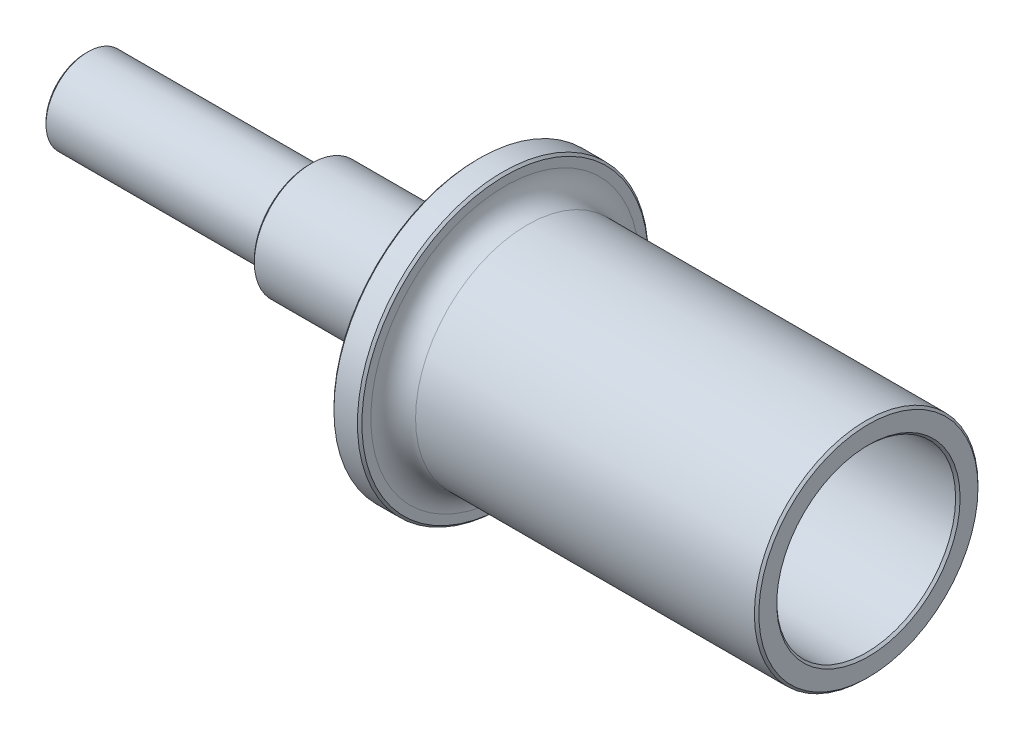
SolidWorks part; units mm, degrees
material "Plain Carbon Steel"
ref_plane "Front Plane" through (0, 0, 0) normal (0, 0, 1) x (1, 0, 0)
ref_plane "Top Plane" through (0, 0, 0) normal (0, 1, 0) x (1, 0, 0)
ref_plane "Right Plane" through (0, 0, 0) normal (1, 0, 0) x (0, 0, -1)
sketch "Sketch1" plane through (0, 0, 0) normal (0, 1, 0) x (1, 0, 0)
  line L0 (6.35, 10.16) -> (-31.6365, 10.16)
  line L1 (6.35, 10.16) -> (6.35, 12.7)
  line L2 (-38.1, 16.51) -> (-34.925, 16.51)
  line L3 (-38.1, 16.51) -> (-38.1, 6.5)
  line L4 (-38.1, 6.5) -> (-57.15, 6.5)
  line L5 (-57.15, 6.5) -> (-57.15, 4.7625)
  line L6 (-57.15, 4.7625) -> (-82.55, 4.7625)
  line L7 (-82.55, 0) -> (-82.55, 4.7625)
  line L8 (-34.1765, 7.62) -> (-34.1765, 0)
  line L9 (-34.925, 16.51) -> (-34.925, 15.24)
  line L10 (-32.385, 12.7) -> (6.35, 12.7)
  line L11 (0, 0) -> (-98.3982, 0) construction
  line L12 (-82.55, 0) -> (-34.1765, 0)
  arc A0 (-34.925, 15.24) -> (-32.385, 12.7) centre (-32.385, 15.24) ccw
  arc A1 (-31.6365, 10.16) -> (-34.1765, 7.62) centre (-31.6365, 7.62) ccw
  dimension "D12" = 3.175
  dimension "D13" = 2.54
  dimension "D2" = 6.5
  dimension "D3" = 25.4
  dimension "D4" = 4.7625
  dimension "D5" = 2.54
  dimension "D6" = 3.9235
  dimension "D7" = 16.51
  dimension "D8" = 44.45
  dimension "D9" = 19.05
  dimension "D10" = 12.7
  dimension "D11" = 38.1
revolve "Revolve1" add sketch "Sketch1" angle 360 about L11
cosmetic thread "Cosmetic Thread1" parameters "D2"=8.255
sketch "Sketch3" plane through (0, 0, 0) normal (1, 0, 0) x (0, 0, -1)
  line L0 (-13.7014, 0) -> (14.6346, 0)
sketch "Sketch5" plane through (0, 0, 0) normal (0, 1, 0) x (1, 0, 0)
  line L0 (-55.8, 0) -> (-74.927, 0) construction
  line L1 (-55.8, 0) -> (-55.8, 5.8985) construction
  line L2 (-55.8, 0) -> (-55.8, 5.8985) construction
  line L3 (-82.55, 4.7625) -> (-82.55, -4.7625) construction
  line L4 (-82.55, 4.7625) -> (-82.55, -4.7625) construction
  line L5 (-55.8, 0) -> (-74.927, 0) construction
fillet "Fillet2" radius 0.75 2 edges at (-57.15, 0, -4.7625) (-38.1, 0, -6.5)
chamfer "Chamfer1" distance 0.254 angle 45 6 edges at (-82.55, 0, -4.7625) (6.35, 0, -10.16) (6.35, 0, -12.7) (-57.15, 0, -6.5) (-38.1, 0, -16.51) (-34.925, 0, -16.51)
